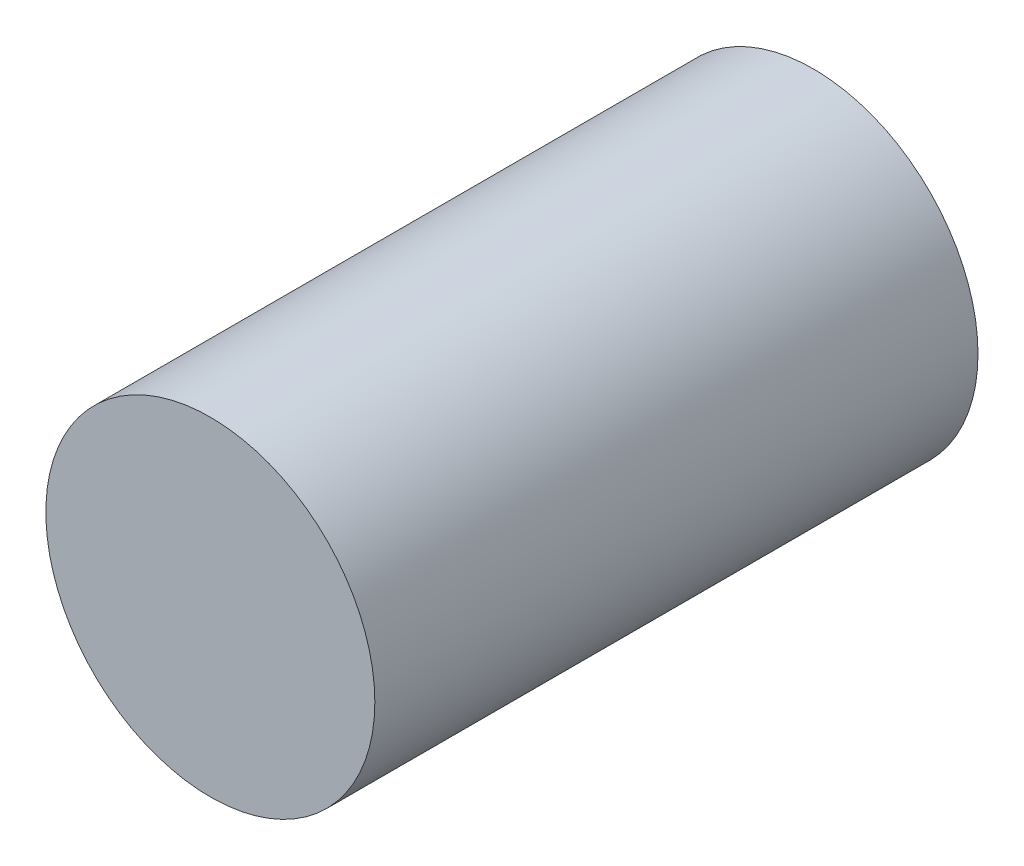
SolidWorks part; units mm, degrees
ref_plane "Plan de face" through (0, 0, 0) normal (0, 0, 1) x (1, 0, 0)
ref_plane "Plan de dessus" through (0, 0, 0) normal (0, 1, 0) x (1, 0, 0)
ref_plane "Plan de droite" through (0, 0, 0) normal (1, 0, 0) x (0, 0, -1)
sketch "Esquisse2" plane through (0, 0, 0) normal (0, 0, 1) x (1, 0, 0)
  circle A0 centre (0, 0) radius 15
  dimension "D1" = 30
extrude "Boss.-Extru.1" add sketch "Esquisse2" along normal blind 55
